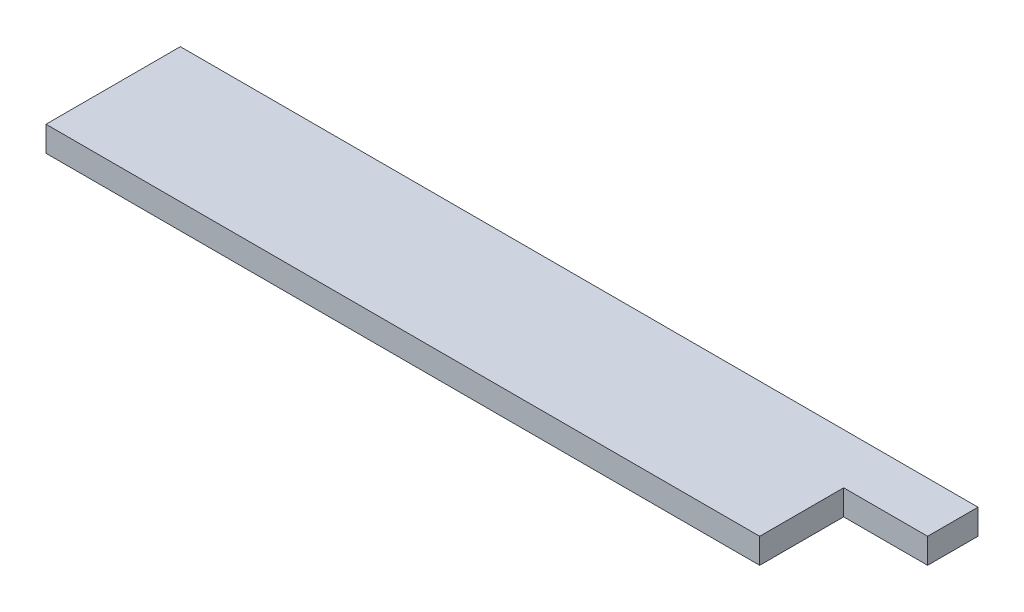
SolidWorks part; units mm, degrees
ref_plane "Alzado" through (0, 0, 0) normal (0, 0, 1) x (1, 0, 0)
ref_plane "Planta" through (0, 0, 0) normal (0, 1, 0) x (1, 0, 0)
ref_plane "Vista lateral" through (0, 0, 0) normal (1, 0, 0) x (0, 0, -1)
sketch "Croquis1" plane through (0, 0, 0) normal (0, 1, 0) x (1, 0, 0)
  line L1 (-47.5, -8) -> (47.5, -8)
  line L2 (-47.5, -8) -> (-47.5, 8)
  line L3 (-47.5, 8) -> (47.5, 8)
  line L4 (47.5, -8) -> (47.5, 8)
  line L5 (-47.5, -8) -> (47.5, 8) construction
  line L6 (-47.5, 8) -> (47.5, -8) construction
  point P0 (0, 0)
  dimension "D1" = 95
  dimension "D2" = 16
extrude "Saliente-Extruir1" add sketch "Croquis1" along normal blind 3
sketch "Croquis2" plane through (0, 3, 0) normal (0, 1, 0) x (1, 0, 0)
  line L1 (47.5, -8) -> (37.5, -8)
  line L2 (47.5, -8) -> (47.5, 2)
  line L3 (47.5, 2) -> (37.5, 2)
  line L4 (37.5, -8) -> (37.5, 2)
  dimension "D1" = 10
  dimension "D2" = 10
extrude "Cortar-Extruir1" cut sketch "Croquis2" against normal blind 10
